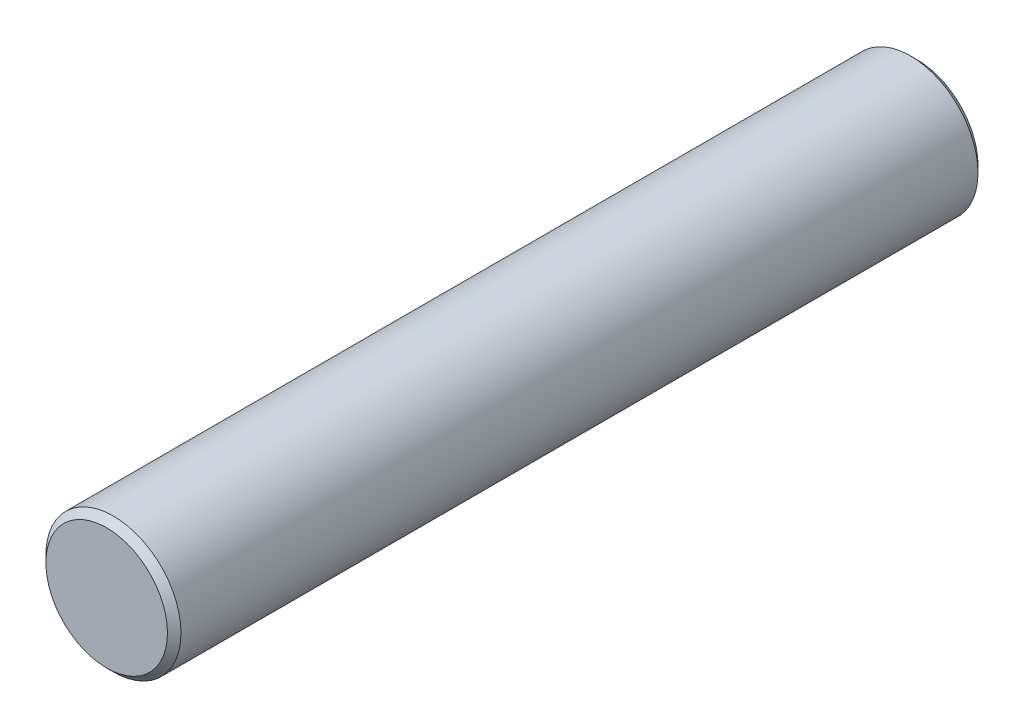
SolidWorks part; units mm, degrees
material "Alloy Steel"
ref_plane "Front Plane" through (0, 0, 0) normal (0, 0, 1) x (1, 0, 0)
ref_plane "Top Plane" through (0, 0, 0) normal (0, 1, 0) x (1, 0, 0)
ref_plane "Right Plane" through (0, 0, 0) normal (1, 0, 0) x (0, 0, -1)
sketch "Sketch1" plane through (0, 0, 0) normal (0, 0, 1) x (1, 0, 0)
  circle A0 centre (0, 0) radius 2.5
  dimension "D1" = 5
extrude "Boss-Extrude1" add sketch "Sketch1" along normal blind 30
chamfer "Chamfer1" distance 0.25 angle 45 2 edges at (2.5, 0, 0) (2.5, 0, 30)
